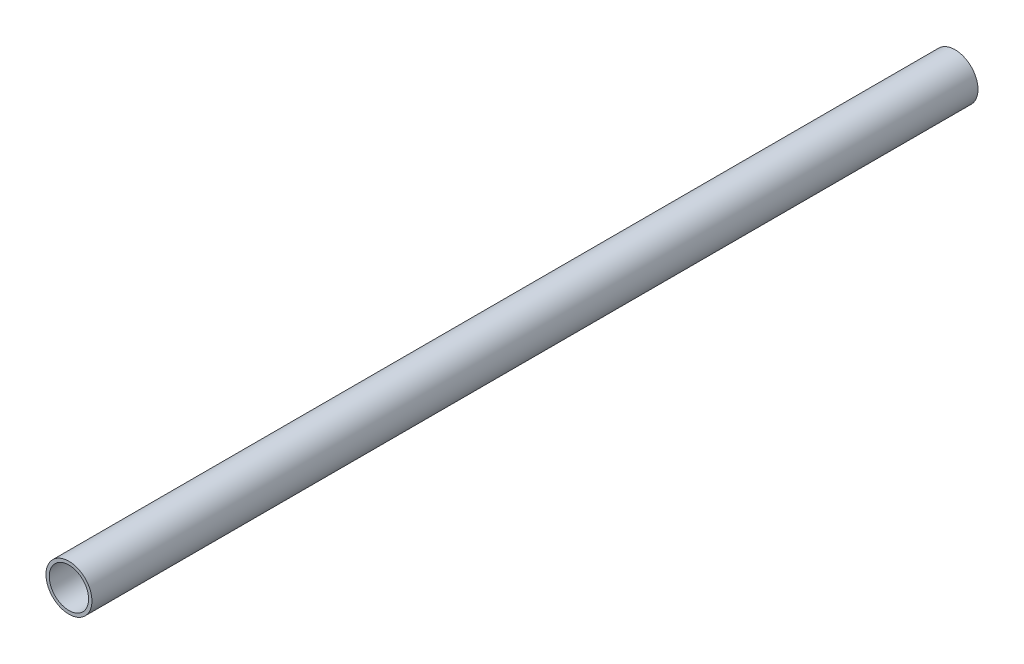
SolidWorks part; units mm, degrees
ref_plane "Front Plane" through (0, 0, 0) normal (0, 0, 1) x (1, 0, 0)
ref_plane "Top Plane" through (0, 0, 0) normal (0, 1, 0) x (1, 0, 0)
ref_plane "Right Plane" through (0, 0, 0) normal (1, 0, 0) x (0, 0, -1)
sketch "Sketch1" plane through (0, 0, 0) normal (0, 0, 1) x (1, 0, 0)
  circle A0 centre (0, 0) radius 7
  dimension "D1" = 14
extrude "Boss-Extrude1" add sketch "Sketch1" along normal blind 270
sketch "Sketch2" plane through (0, 0, 270) normal (0, 0, 1) x (1, 0, 0)
  circle A0 centre (0, 0) radius 6
  dimension "D1" = 12
extrude "Cut-Extrude1" cut sketch "Sketch2" against normal through all
